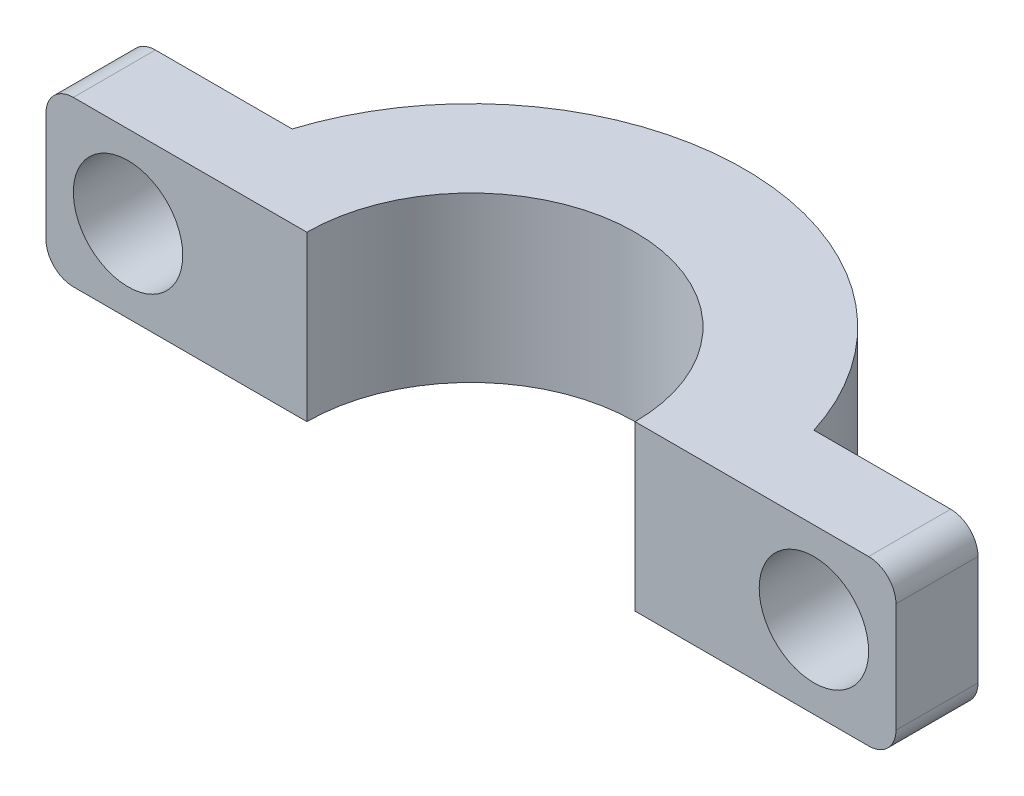
SolidWorks part; units mm, degrees
material "ABS"
ref_plane "Front Plane" through (0, 0, 0) normal (0, 0, 1) x (1, 0, 0)
ref_plane "Top Plane" through (0, 0, 0) normal (0, 1, 0) x (1, 0, 0)
ref_plane "Right Plane" through (0, 0, 0) normal (1, 0, 0) x (0, 0, -1)
sketch "Sketch1" plane through (0, 0, 0) normal (0, 1, 0) x (1, 0, 0)
  line L0 (-10, 0) -> (-6, 0)
  line L1 (6, 0) -> (10, 0)
  arc A0 (-6, 0) -> (6, 0) centre (0, 0) cw
  arc A1 (-10, 0) -> (10, 0) centre (0, 0) cw
  dimension "D1" = 6
  dimension "D3" = 4
extrude "Boss-Extrude1" add sketch "Sketch1" along normal blind 6
sketch "Sketch3" plane through (0, 6, 0) normal (0, 1, 0) x (1, 0, 0)
  line L0 (-10, 0) -> (-15.5394, 0)
  line L1 (-15.5394, 0) -> (-15.5394, 3)
  line L2 (-15.5394, 3) -> (-9.5394, 3)
  line L3 (-10, 0) -> (-6, 0) construction
  arc A0 (10, 0) -> (-10, 0) centre (0, 0) ccw construction
  arc A1 (-9.5394, 3) -> (-10, 0) centre (0, 0) ccw
  dimension "D1" = 3
  dimension "D2" = 6
extrude "Boss-Extrude2" add sketch "Sketch3" against normal up to surface (6 mm away) up to face at (0, 0, -4)
sketch "Sketch4" plane through (0, 0, 0) normal (0, 0, 1) x (1, 0, 0)
  line L0 (-15.5394, 3) -> (10, 3) construction
  line L1 (-15.5394, 0) -> (-15.5394, 6) construction
  line L2 (10, 0) -> (10, 6) construction
  line L3 (-12.5394, 6) -> (-12.5394, 0) construction
  line L4 (-15.5394, 6) -> (-6, 6) construction
  line L5 (-15.5394, 0) -> (-6, 0) construction
  circle A0 centre (-12.5394, 3) radius 2
  point P15 (-12.5394, 3)
  dimension "D1" = 4
  dimension "D2" = 3
extrude "Cut-Extrude2" cut sketch "Sketch4" against normal through all
mirror "Mirror2" about plane through (0, 0, 0) normal (1, 0, 0) of "Boss-Extrude2", "Cut-Extrude2"
fillet "Fillet1" radius 1 4 edges at (-15.5394, 0, -1.5) (-15.5394, 6, -1.5) (15.5394, 0, -1.5) (15.5394, 6, -1.5)
